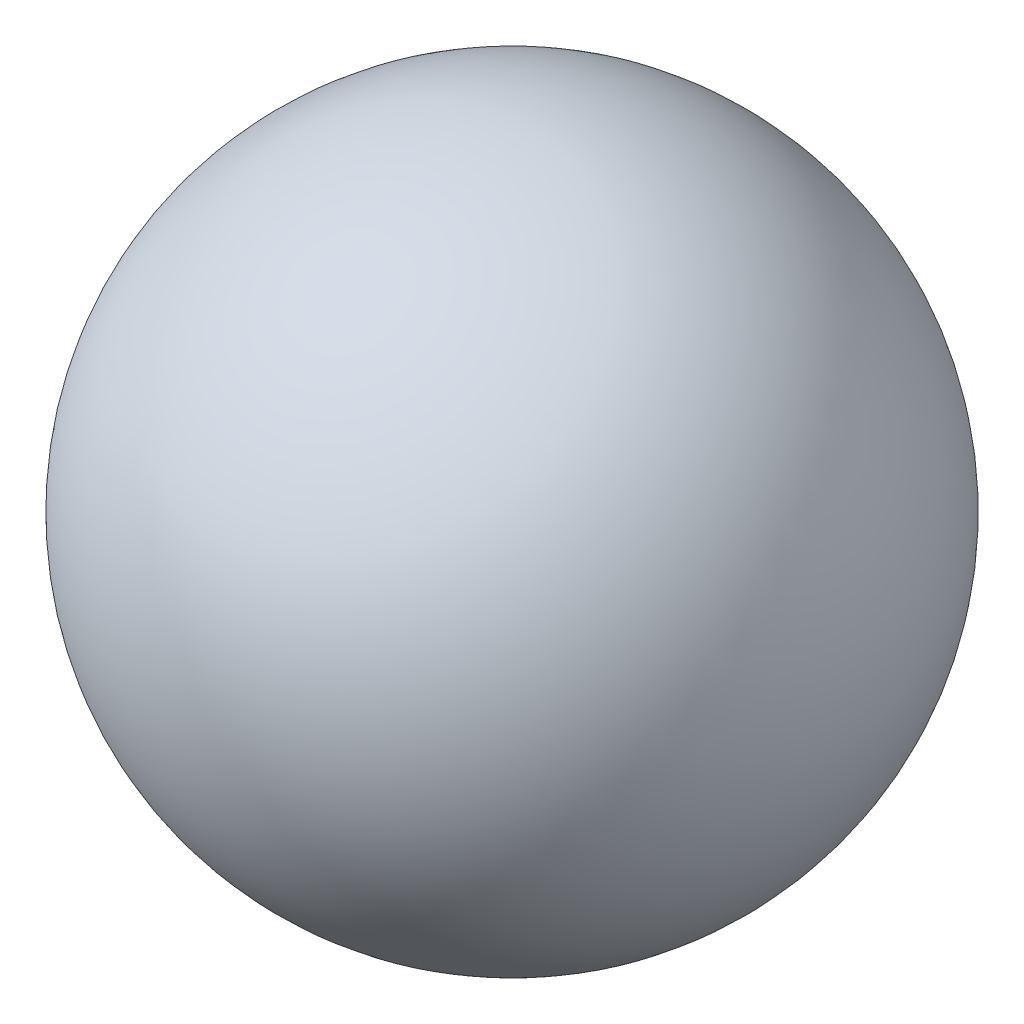
SolidWorks part; units mm, degrees
ref_plane "Front Plane" through (0, 0, 0) normal (0, 0, 1) x (1, 0, 0)
ref_plane "Top Plane" through (0, 0, 0) normal (0, 1, 0) x (1, 0, 0)
ref_plane "Right Plane" through (0, 0, 0) normal (1, 0, 0) x (0, 0, -1)
sketch "Sketch1" plane through (0, 0, 0) normal (0, 0, 1) x (1, 0, 0)
  line L0 (0, 50) -> (0, -50)
  arc A0 (0, 50) -> (0, -50) centre (0, 0) ccw
  dimension "D1" = 100
revolve "Revolve1" add sketch "Sketch1" angle 360 about L0
